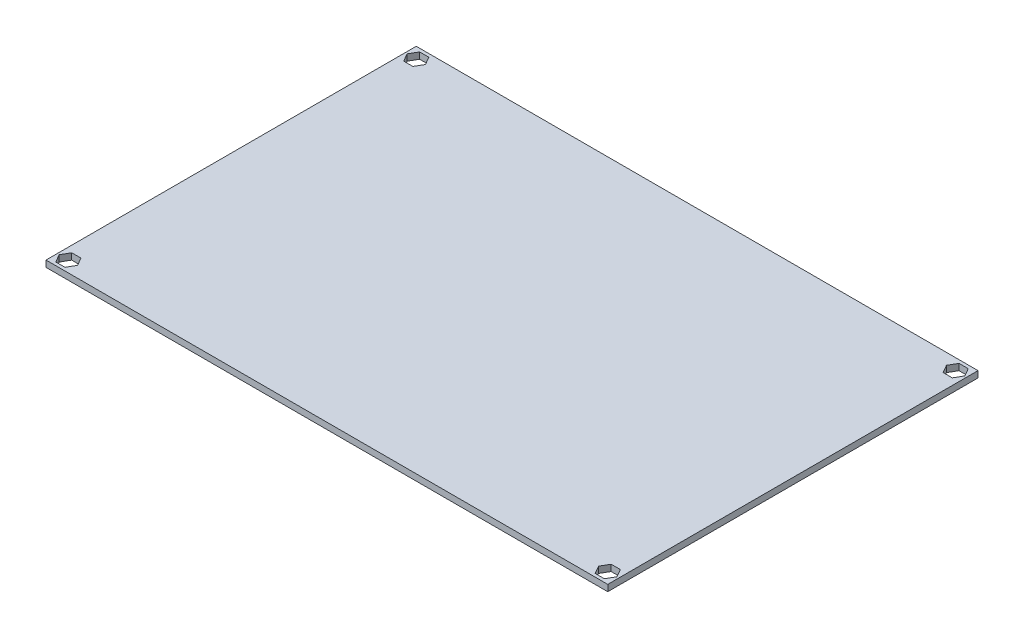
SolidWorks part; units mm, degrees
ref_plane "Front Plane" through (0, 0, 0) normal (0, 0, 1) x (1, 0, 0)
ref_plane "Top Plane" through (0, 0, 0) normal (0, 1, 0) x (1, 0, 0)
ref_plane "Right Plane" through (0, 0, 0) normal (1, 0, 0) x (0, 0, -1)
sketch "Sketch1" plane through (0, 0, 0) normal (0, 1, 0) x (1, 0, 0)
  line L1 (-80.2193, 70.144) -> (95.7807, 70.144)
  line L2 (-80.2193, 70.144) -> (-80.2193, -45.856)
  line L3 (-80.2193, -45.856) -> (95.7807, -45.856)
  line L4 (95.7807, 70.144) -> (95.7807, -45.856)
  dimension "D1" = 176
  dimension "D2" = 116
extrude "Boss-Extrude1" add sketch "Sketch1" along normal blind 2
sketch "Sketch3" plane through (0, 2, 0) normal (0, 1, 0) x (1, 0, 0)
  line L0 (95.7807, 70.144) -> (-80.2193, 70.144) construction
  line L1 (-80.2193, 70.144) -> (-80.2193, -45.856) construction
  line L2 (-75.2759, 64.144) -> (-73.8325, 66.644)
  line L3 (-73.8325, 66.644) -> (-75.2759, 69.144)
  line L4 (-75.2759, 69.144) -> (-78.1627, 69.144)
  line L5 (-78.1627, 69.144) -> (-79.606, 66.644)
  line L6 (-79.606, 66.644) -> (-78.1627, 64.144)
  line L7 (-78.1627, 64.144) -> (-75.2759, 64.144)
  line L8 (7.7807, 70.144) -> (7.7807, -45.856) construction
  line L9 (-80.2193, -45.856) -> (95.7807, -45.856) construction
  line L10 (-80.2193, 12.144) -> (95.7807, 12.144) construction
  line L11 (95.7807, -45.856) -> (95.7807, 70.144) construction
  line L12 (93.7241, 64.144) -> (90.8373, 64.144)
  line L13 (95.1675, 66.644) -> (93.7241, 64.144)
  line L14 (93.7241, 69.144) -> (95.1675, 66.644)
  line L15 (90.8373, 69.144) -> (93.7241, 69.144)
  line L16 (89.394, 66.644) -> (90.8373, 69.144)
  line L17 (90.8373, 64.144) -> (89.394, 66.644)
  line L18 (90.8373, -39.856) -> (89.394, -42.356)
  line L19 (89.394, -42.356) -> (90.8373, -44.856)
  line L20 (90.8373, -44.856) -> (93.7241, -44.856)
  line L21 (93.7241, -44.856) -> (95.1675, -42.356)
  line L22 (95.1675, -42.356) -> (93.7241, -39.856)
  line L23 (93.7241, -39.856) -> (90.8373, -39.856)
  line L24 (-78.1627, -39.856) -> (-75.2759, -39.856)
  line L25 (-79.606, -42.356) -> (-78.1627, -39.856)
  line L26 (-78.1627, -44.856) -> (-79.606, -42.356)
  line L27 (-75.2759, -44.856) -> (-78.1627, -44.856)
  line L28 (-73.8325, -42.356) -> (-75.2759, -44.856)
  line L29 (-75.2759, -39.856) -> (-73.8325, -42.356)
  circle A0 centre (-76.7193, 66.644) radius 2.5 construction
  circle A1 centre (92.2807, 66.644) radius 2.5 construction
  circle A2 centre (92.2807, -42.356) radius 2.5 construction
  circle A3 centre (-76.7193, -42.356) radius 2.5 construction
  dimension "D1" = 3.5
  dimension "D2" = 3.5
extrude "Cut-Extrude2" cut sketch "Sketch3" against normal blind 2
